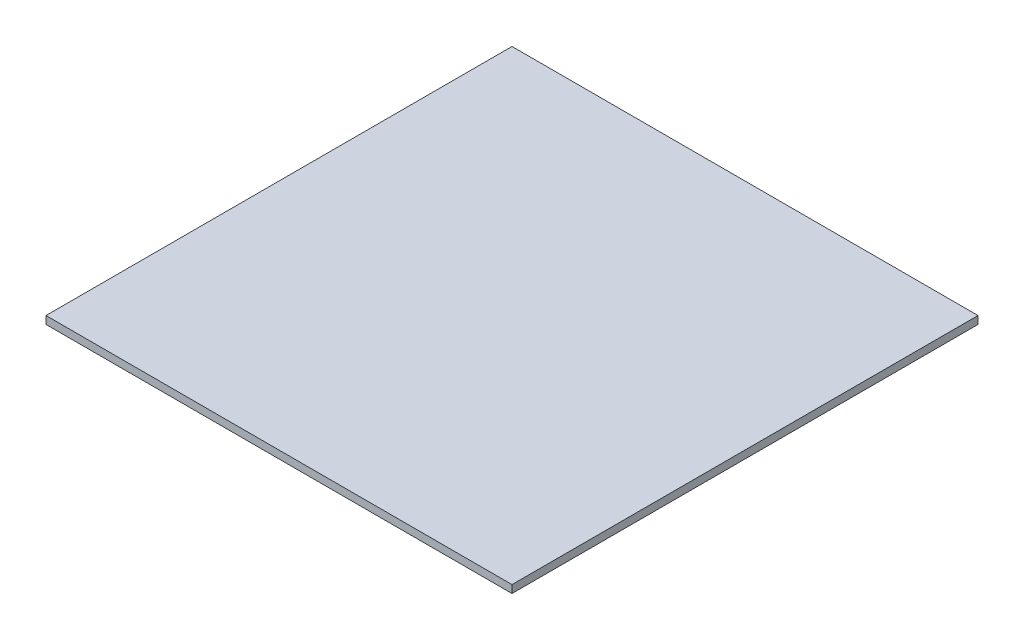
SolidWorks part; units mm, degrees
ref_plane "Front Plane" through (0, 0, 0) normal (0, 0, 1) x (1, 0, 0)
ref_plane "Top Plane" through (0, 0, 0) normal (0, 1, 0) x (1, 0, 0)
ref_plane "Right Plane" through (0, 0, 0) normal (1, 0, 0) x (0, 0, -1)
sketch "Sketch1" plane through (0, 0, 0) normal (0, 1, 0) x (1, 0, 0)
  line L1 (0, 0) -> (609.6, 0)
  line L2 (0, 0) -> (0, 609.6)
  line L3 (0, 609.6) -> (609.6, 609.6)
  line L4 (609.6, 0) -> (609.6, 609.6)
  dimension "D1" = 609.6
  dimension "D2" = 609.6
extrude "Boss-Extrude1" add sketch "Sketch1" along normal blind 10.16
